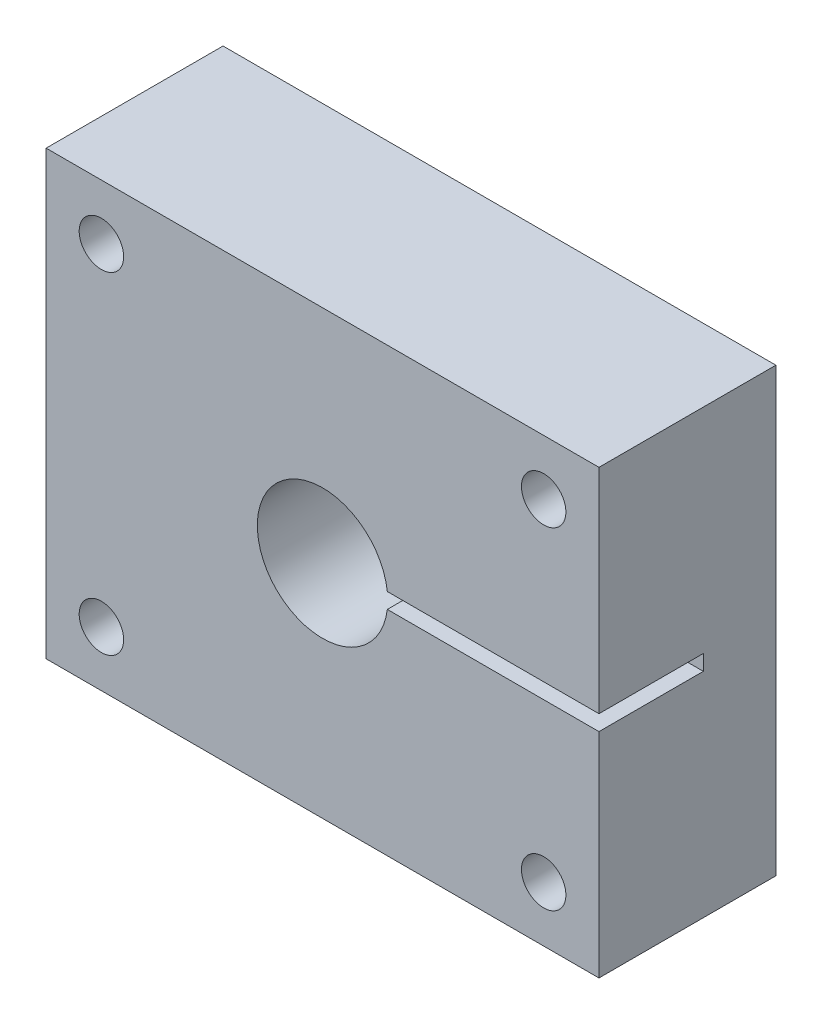
SolidWorks part; units mm, degrees
ref_plane "Front Plane" through (0, 0, 0) normal (0, 0, 1) x (1, 0, 0)
ref_plane "Top Plane" through (0, 0, 0) normal (0, 1, 0) x (1, 0, 0)
ref_plane "Right Plane" through (0, 0, 0) normal (1, 0, 0) x (0, 0, -1)
sketch "Sketch1" plane through (0, 0, 0) normal (0, 0, 1) x (1, 0, 0)
  line L1 (-31.75, 25.4) -> (31.75, 25.4)
  line L2 (-31.75, 25.4) -> (-31.75, -25.4)
  line L3 (-31.75, -25.4) -> (31.75, -25.4)
  line L4 (31.75, 25.4) -> (31.75, -25.4)
  line L5 (-31.75, 25.4) -> (31.75, -25.4) construction
  line L6 (-31.75, -25.4) -> (31.75, 25.4) construction
  point P0 (0, 0)
  dimension "D1" = 63.5
  dimension "D2" = 50.8
extrude "Boss-Extrude1" add sketch "Sketch1" along normal blind 20.32
sketch "Sketch2" plane through (0, 0, 20.32) normal (0, 0, 1) x (1, 0, 0)
  circle A0 centre (0, 0) radius 7.493
  dimension "D1" = 14.986
extrude "Cut-Extrude1" cut sketch "Sketch2" against normal blind 11.9888
sketch "Sketch3" plane through (0, 0, 20.32) normal (0, 0, 1) x (1, 0, 0)
  line L0 (31.75, -25.4) -> (31.75, 25.4) construction
  line L1 (0, 0.889) -> (31.75, 0.889)
  line L2 (0, 0.889) -> (0, -0.889)
  line L3 (0, -0.889) -> (31.75, -0.889)
  line L4 (31.75, 0.889) -> (31.75, -0.889)
  point P6 (0, 0)
  dimension "D1" = 1.778
extrude "Cut-Extrude2" cut sketch "Sketch3" against normal blind 11.9888
sketch "Sketch9" plane through (0, 0, 8.3312) normal (0, 0, 1) x (1, 0, 0)
  circle A0 centre (0, 0) radius 1.9939
  dimension "D1" = 3.9878
extrude "Cut-Extrude3" cut sketch "Sketch9" against normal blind 11.9888
ref_plane "Plane2" through (0, 0, 6.3312) normal (0, 0, 1) x (1, 0, 0)
sketch "Sketch10" plane through (0, 0, 0) normal (0, 0, -1) x (-1, 0, 0)
  circle A1 centre (0, 0) radius 7.493
  circle A2 centre (0, 0) radius 7.493
  dimension "D1" = 0
extrude "Cut-Extrude4" cut sketch "Sketch10" against normal up to surface (6.3312 mm away)
sketch "Sketch11" plane through (0, 0, 20.32) normal (0, 0, 1) x (1, 0, 0)
  line L1 (-25.4, 19.05) -> (25.4, 19.05) construction
  line L2 (-25.4, 19.05) -> (-25.4, -19.05) construction
  line L3 (-25.4, -19.05) -> (25.4, -19.05) construction
  line L4 (25.4, 19.05) -> (25.4, -19.05) construction
  line L5 (-25.4, 19.05) -> (25.4, -19.05) construction
  line L6 (-25.4, -19.05) -> (25.4, 19.05) construction
  circle A0 centre (-25.4, 19.05) radius 2.5527
  point P0 (0, 0)
  dimension "D3" = 5.1054
  dimension "D1" = 50.8
  dimension "D2" = 38.1
extrude "Cut-Extrude5" cut sketch "Sketch11" against normal through all
mirror "Mirror1" about plane through (0, 0, 0) normal (1, 0, 0) of "Cut-Extrude5"
mirror "Mirror2" about plane through (0, 0, 0) normal (0, 1, 0) of "Mirror1", "Cut-Extrude5"
